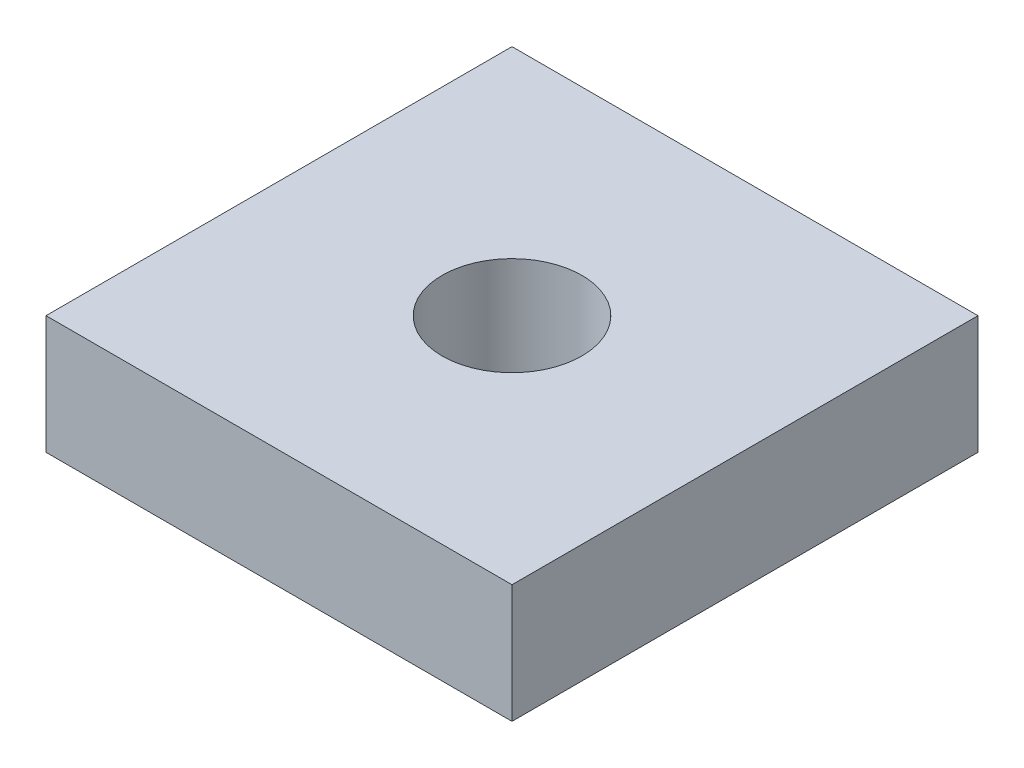
SolidWorks part; units mm, degrees
ref_plane "Front Plane" through (0, 0, 0) normal (0, 0, 1) x (1, 0, 0)
ref_plane "Top Plane" through (0, 0, 0) normal (0, 1, 0) x (1, 0, 0)
ref_plane "Right Plane" through (0, 0, 0) normal (1, 0, 0) x (0, 0, -1)
sketch "Sketch1" plane through (0, 0, 0) normal (0, 1, 0) x (1, 0, 0)
  line L1 (-4.0514, 3.5531) -> (5.9486, 3.5531)
  line L2 (-4.0514, 3.5531) -> (-4.0514, -6.4469)
  line L3 (-4.0514, -6.4469) -> (5.9486, -6.4469)
  line L4 (5.9486, 3.5531) -> (5.9486, -6.4469)
  circle A0 centre (0.9486, -1.4469) radius 1.5
  point P8 (-24.791, 12.6527)
  dimension "D3" = 3
  dimension "D1" = 10
  dimension "D2" = 10
  dimension "D4" = 5
  dimension "D5" = 5
extrude "Boss-Extrude1" add sketch "Sketch1" along normal blind 2.54
